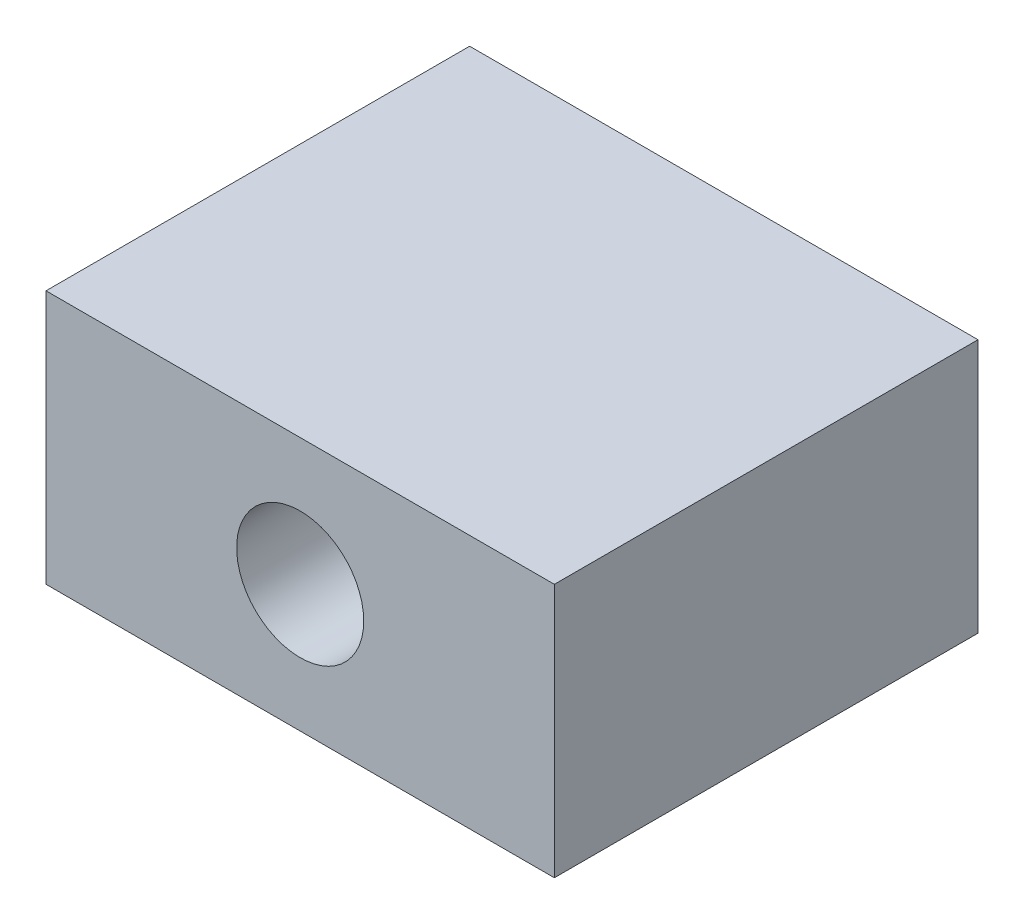
SolidWorks part; units mm, degrees
ref_plane "Front Plane" through (0, 0, 0) normal (0, 0, 1) x (1, 0, 0)
ref_plane "Top Plane" through (0, 0, 0) normal (0, 1, 0) x (1, 0, 0)
ref_plane "Right Plane" through (0, 0, 0) normal (1, 0, 0) x (0, 0, -1)
sketch "Sketch1" plane through (0, 0, 0) normal (0, 0, 1) x (1, 0, 0)
  line L1 (220, 15) -> (280, 15)
  line L2 (220, 15) -> (220, -15)
  line L3 (220, -15) -> (280, -15)
  line L4 (280, 15) -> (280, -15)
  line L5 (220, 15) -> (280, -15) construction
  line L6 (220, -15) -> (280, 15) construction
  circle A0 centre (250, 0) radius 4
  circle A1 centre (250, 0) radius 7.5
  dimension "D1" = 8
  dimension "D2" = 15
  dimension "D3" = 250
  dimension "D4" = 60
  dimension "D5" = 30
extrude "Boss-Extrude1" add sketch "Sketch1" along normal mid plane 50 contours L4 L1 L2 L3 A1
sketch "Sketch2" plane through (220, 0, 0) normal (-1, 0, 0) x (0, 0, 1)
  circle A1 centre (13.5, 0) radius 2.5
  circle A2 centre (-13.5, 0) radius 2.5
  point P5 (0, 0)
  point P7 (-2.9595, -6.4583)
  dimension "D1" = 5
  dimension "D2" = 27
  dimension "D3" = 13.5
extrude "Cut-Extrude1" cut sketch "Sketch2" against normal blind 30
